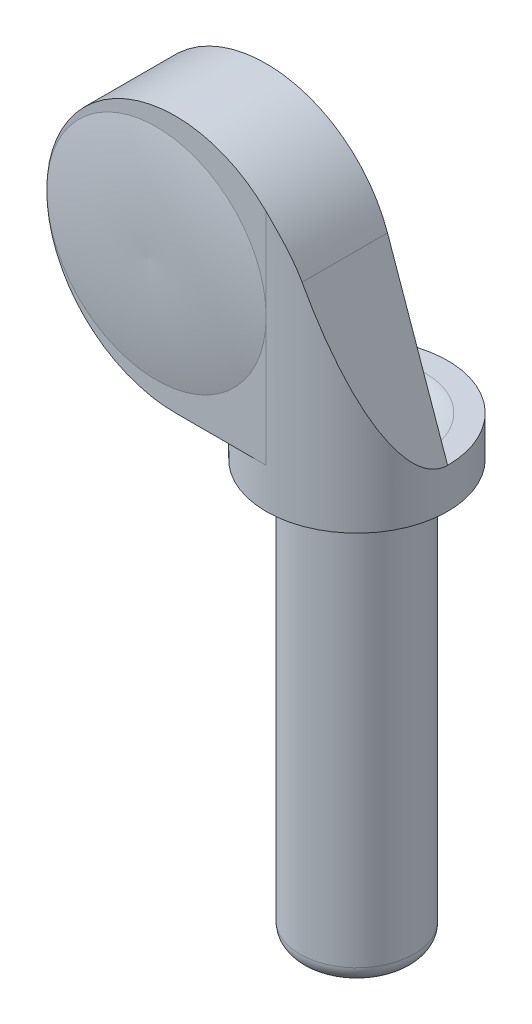
SolidWorks part; units mm, degrees
ref_plane "前视基准面" through (0, 0, 0) normal (0, 0, 1) x (1, 0, 0)
ref_plane "上视基准面" through (0, 0, 0) normal (0, 1, 0) x (1, 0, 0)
ref_plane "右视基准面" through (0, 0, 0) normal (1, 0, 0) x (0, 0, -1)
sketch "草图1" plane through (0, 0, 0) normal (0, 1, 0) x (1, 0, 0)
  line L0 (0, 0) -> (0, 4.3268) construction
  line L1 (0, 0) -> (6.0935, 0) construction
  circle A0 centre (0, 0) radius 2
  dimension "D1" = 4
extrude "凸台-拉伸1" add sketch "草图1" along normal blind 16
sketch "草图2" plane through (0, 0, 0) normal (0, 0, 1) x (1, 0, 0)
  line L0 (-2, 19.9066) -> (-2, 24.8439) construction
  line L1 (-2, 16) -> (-2, 0) construction
  line L2 (-2.327, 16) -> (-3.6912, 16) construction
  line L3 (2, 16) -> (-2, 16) construction
  line L4 (3.175, 16) -> (1.0707, 21.9912)
  line L5 (3.175, 16) -> (-3.175, 16)
  line L6 (0, 19.5869) -> (0, 22.2425) construction
  arc A0 (1.0707, 21.9912) -> (-3.175, 16) centre (-3.175, 20.5) ccw
  dimension "D1" = 4.5
  dimension "D2" = 9
  dimension "D3" = 3.175
  dimension "D4" = 1.175
extrude "凸台-拉伸2" add sketch "草图2" along normal blind 3.175
sketch "草图4" plane through (0, 0, 0) normal (0, 0, -1) x (-1, 0, 0)
  circle A0 centre (3.175, 20.5) radius 3.15
  dimension "D1" = 6.3
extrude "切除-拉伸6" cut sketch "草图4" against normal blind 2.775
fillet "圆角3" radius 0.6 1 edges at (0, 0, 2)
sketch "草图7" plane through (0, 16, 0) normal (0, 1, 0) x (1, 0, 0)
  circle A0 centre (0, 0) radius 3.175
  dimension "D1" = 6.35
extrude "凸台-拉伸3" add sketch "草图7" against normal blind 1.4
sketch "草图11" plane through (0, 16, 0) normal (0, -1, 0) x (1, 0, 0)
  line L0 (3.175, 3.175) -> (3.506, 0.275)
  line L1 (3.175, 3.175) -> (0, 3.175)
  line L2 (3.506, 0.275) -> (3.175, 0)
  arc A0 (0, 3.175) -> (3.175, 0) centre (0, 0) cw
  circle A1 centre (0, 0) radius 3.175 construction
extrude "切除-拉伸10" cut sketch "草图11" against normal through all
ref_plane "基准面1" through (0, 20.5, 0) normal (0, -1, 0) x (-1, 0, 0)
sketch "草图12" plane through (0, 20.5, 0) normal (0, -1, 0) x (-1, 0, 0)
  line L0 (3.8375, -3.175) -> (3.8375, -3.475)
  line L1 (0, -3.175) -> (7.675, -3.175) construction
  line L2 (3.8375, -3.175) -> (7.675, -3.175)
  arc A0 (7.675, -3.175) -> (3.8375, -3.475) centre (4.5306, 12.3533) cw
  dimension "D1" = 0.3
revolve "旋转1" add sketch "草图12" angle 360 about L0
fillet "圆角4" radius 0.3 1 edges at (-6.325, 20.5, 0)
sketch "草图13" plane through (0, 16, 0) normal (0, 1, 0) x (1, 0, 0)
  line L0 (-3.5731, 0) -> (4.3556, 0) construction
  line L1 (0.275, 0) -> (-6.625, 0) construction
  line L2 (-1.4, 0) -> (1.4, 0)
  arc A0 (1.4, 0) -> (-1.4, 0) centre (0, 0) ccw
  dimension "D1" = 2.8
extrude "切除-拉伸11" cut sketch "草图13" against normal up to next
fillet "圆角5" radius 1 1 edges at (0, 16, -1.4)
